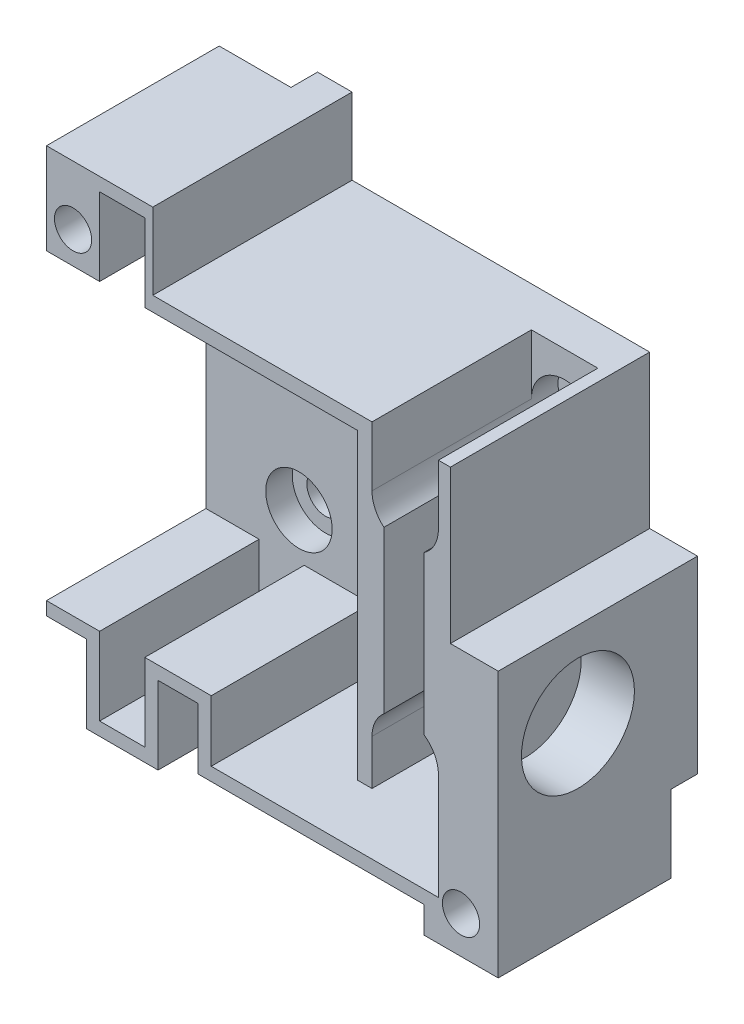
SolidWorks part; units mm, degrees
ref_plane "Front Plane" through (0, 0, 0) normal (0, 0, 1) x (1, 0, 0)
ref_plane "Top Plane" through (0, 0, 0) normal (0, 1, 0) x (1, 0, 0)
ref_plane "Right Plane" through (0, 0, 0) normal (1, 0, 0) x (0, 0, -1)
sketch "Sketch1" plane through (0, 0, 0) normal (0, 0, 1) x (1, 0, 0)
  line L1 (-17, 19) -> (17, 19)
  line L2 (-17, 19) -> (-17, -19)
  line L3 (-17, -19) -> (17, -19)
  line L4 (17, 19) -> (17, -19)
  line L5 (-17, 19) -> (17, -19) construction
  line L6 (-17, -19) -> (17, 19) construction
  point P0 (0, 0)
  dimension "D1" = 38
  dimension "D2" = 34
extrude "Boss-Extrude1" add sketch "Sketch1" along normal blind 16
sketch "Sketch2" plane through (0, 0, 16) normal (0, 0, 1) x (1, 0, 0)
  line L0 (0, 0) -> (-17, 0) construction
  line L5 (-17, 11.4) -> (5.4, 11.4)
  line L6 (-17, 11.4) -> (-17, -11.4)
  line L7 (-17, -11.4) -> (5.4, -11.4)
  line L8 (5.4, 11.4) -> (5.4, -11.4)
  line L9 (-17, 11.4) -> (5.4, -11.4) construction
  line L10 (-17, -11.4) -> (5.4, 11.4) construction
  line L11 (-17, 19) -> (-17, -19) construction
  line L12 (-10.6, -11.4) -> (-10.6, -16.25)
  line L13 (-13, 11.4) -> (-10.6, 11.4)
  line L14 (-13, 11.4) -> (-13, 16.25)
  line L15 (-13, 16.25) -> (-10.6, 16.25)
  line L16 (-10.6, 11.4) -> (-10.6, 16.25)
  line L17 (-13, -11.4) -> (-13, -16.25)
  line L18 (-13, -16.25) -> (-10.6, -16.25)
  line L21 (-17, -11.4) -> (-17, 4.4)
  point P0 (-5.8, 0)
  dimension "D1" = 22.4
  dimension "D2" = 22.8
  dimension "D3" = 5.8
  dimension "D4" = 4
  dimension "D5" = 2.4
  dimension "D6" = 4.85
extrude "Cut-Extrude1" cut sketch "Sketch2" against normal blind 13 contours L8 L5 L6 L7 | L17 L18 L12 L7 | L5 L16 L15 L14
sketch "Sketch3" plane through (0, 0, 16) normal (0, 0, 1) x (1, 0, 0)
  line L1 (5.4, -11.4) -> (-4.6, -11.4)
  line L2 (5.4, -11.4) -> (5.4, -16)
  line L3 (5.4, -16) -> (-4.6, -16)
  line L4 (-4.6, -11.4) -> (-4.6, -16)
  line L5 (5.4, -16) -> (8.4, -16)
  line L6 (5.4, -16) -> (5.4, -11.4)
  line L7 (5.4, -11.4) -> (8.4, -11.4)
  line L8 (8.4, -16) -> (8.4, -11.4)
  line L10 (-17, -19) -> (17, -19) construction
  line L11 (17, 19) -> (-17, 19) construction
  line L12 (8.4, -16) -> (11.4, -16)
  line L13 (8.4, -16) -> (8.4, 19)
  line L14 (8.4, 19) -> (11.4, 19)
  line L15 (11.4, -16) -> (11.4, 19)
  line M11 (17, 19) -> (-17, 19)
  line M21 (5.4, -11.4) -> (-10.6, -11.4)
  dimension "D1" = 3
  dimension "D2" = 10
  dimension "D3" = 3
  dimension "D4" = 3
extrude "Cut-Extrude2" cut sketch "Sketch3" against normal blind 13 contours L12 L15 L13 L8 M11 | L4 L3 L2 M21 | L5 L8 L7 L2
sketch "Sketch4" plane through (0, 0, 16) normal (0, 0, 1) x (1, 0, 0)
  line L0 (-17, 19) -> (-17, 11.4) construction
  line L3 (-17, -19) -> (17, -19) construction
  line L4 (17, -19) -> (17, 19) construction
  line L5 (8.4, 19) -> (-17, 19) construction
  circle A0 centre (-15, 13.8) radius 1.4
  circle A1 centre (14.2, -16.2) radius 1.4
  dimension "D2" = 5.2
  dimension "D3" = 2.8
  dimension "D4" = 2.8
  dimension "D5" = 2.8
  dimension "D6" = 2.8
  dimension "D1" = 2
extrude "Cut-Extrude3" cut sketch "Sketch4" against normal through all
sketch "Sketch5" plane through (0, 0, 0) normal (0, 0, -1) x (-1, 0, 0)
  line L0 (-17, 19) -> (17, 19) construction
  line L1 (18.4, 13.8) -> (11.6, 13.8)
  line L2 (18.4, 13.8) -> (18.4, 19)
  line L3 (18.4, 19) -> (11.6, 19)
  line L4 (11.6, 13.8) -> (11.6, 19)
  line L5 (-17, -19) -> (-17, 19) construction
  line L6 (-14.2, -19.2) -> (-17, -19.2)
  line L7 (-14.2, -19.2) -> (-14.2, -13.2)
  line L8 (-14.2, -13.2) -> (-17, -13.2)
  line L9 (-17, -19.2) -> (-17, -13.2)
  line L11 (-14.2, -19.2) -> (-10.2, -19.2)
  line L12 (-14.2, -19.2) -> (-14.2, -13.2)
  line L13 (-14.2, -13.2) -> (-10.2, -13.2)
  line L14 (-10.2, -19.2) -> (-10.2, -13.2)
  circle A0 centre (15, 13.8) radius 3.4
  circle A1 centre (-14.2, -16.2) radius 3
  circle M1 centre (15, 13.8) radius 1.4
  circle M2 centre (-14.2, -16.2) radius 1.4
  line M3 (-17, 19) -> (-17, -19)
  line M4 (-17, -19) -> (17, -19)
  line M5 (17, -19) -> (17, 19)
  line M6 (17, 19) -> (-17, 19)
  dimension "D1" = 6.8
  dimension "D2" = 6
  dimension "D3" = 4
extrude "Cut-Extrude5" cut sketch "Sketch5" against normal blind 2 contours A1 L7 M4 M2 | L7 A1 L9 M4 M2 | A1 M3 M4 | A1 L8 M3 | L9 A1 | A1 L7 M4 | A1 L9 L6 M4 | L7 A1 M4 | A0 L2 L3 M5 | A0 L4 M5 M6 | A0 L1 M5 M1 | L1 A0 M5 | A0 L1 M5 | L1 A0 M5 M1 | A1 L14 L13 M4
sketch "Sketch7" plane through (0, 19, 0) normal (0, 1, 0) x (1, 0, 0)
  line L0 (17, -16) -> (17, 0) construction
  line L1 (-17, -16) -> (17, -16)
  line L2 (-17, -16) -> (-17, -15)
  line L3 (-17, -15) -> (17, -15)
  line L4 (17, -16) -> (17, -15)
  dimension "D1" = 1
extrude "Cut-Extrude6" cut sketch "Sketch7" against normal through all
sketch "Sketch9" plane through (0, 0, 15) normal (0, 0, 1) x (1, 0, 0)
  line L0 (8.4, 19) -> (-17, 19) construction
  line L1 (-9, 19) -> (17, 19)
  line L2 (-9, 19) -> (-9, 12.5)
  line L3 (-9, 12.5) -> (17, 12.5)
  line L4 (17, 19) -> (17, 12.5)
  line L5 (17, -19) -> (17, 19) construction
  line L6 (-17, -19) -> (-17, -11.4) construction
  line L7 (-17, -12.4) -> (-14, -12.4)
  line L8 (-17, -12.4) -> (-17, -19)
  line L9 (-17, -19) -> (-14, -19)
  line L10 (-14, -12.4) -> (-14, -19)
  line L11 (17, -19) -> (-17, -19) construction
  line L12 (-13, -16.25) -> (-10.6, -16.25) construction
  line L13 (-8.6, -19) -> (-5.6, -19)
  line L14 (-8.6, -19) -> (-8.6, -12.4)
  line L15 (-8.6, -12.4) -> (-5.6, -12.4)
  line L16 (-5.6, -19) -> (-5.6, -12.4)
  line L17 (-5.6, -19) -> (11.4, -19)
  line L18 (-5.6, -19) -> (-5.6, -17)
  line L19 (-5.6, -17) -> (11.4, -17)
  line L20 (11.4, -19) -> (11.4, -17)
  line L21 (-14, -19) -> (-8.6, -19)
  line L22 (-14, -19) -> (-14, -18.25)
  line L23 (-10.6, -11.4) -> (-4.6, -11.4) construction
  line L24 (-17, -11.4) -> (-13, -11.4) construction
  line L25 (-10.6, -11.4) -> (-10.6, -16.25) construction
  line L26 (-4.6, -11.4) -> (-4.6, -16) construction
  line L27 (-4.6, -16) -> (11.4, -16) construction
  line L28 (-13, -11.4) -> (-13, -16.25) construction
  line L29 (-14, -18.25) -> (-8.6, -18.25)
  line L30 (-8.6, -19) -> (-8.6, -18.25)
  line L32 (-13, 16.25) -> (-10.6, 16.25) construction
  line L33 (-17, 19) -> (-9, 19)
  line L34 (-17, 19) -> (-17, 18.25)
  line L35 (-17, 18.25) -> (-9, 18.25)
  line L36 (-9, 19) -> (-9, 18.25)
  line L37 (11.4, -16) -> (11.4, 19) construction
  line L38 (17, 19) -> (13.4, 19)
  line L39 (17, 19) -> (17, 1)
  line L40 (17, 1) -> (13.4, 1)
  line L41 (13.4, 19) -> (13.4, 1)
  line M21 (8.4, -11.4) -> (8.4, 19)
  line M22 (8.4, 19) -> (-17, 19)
  line M23 (-17, 19) -> (-17, 11.4)
  dimension "D1" = 6.5
  dimension "D2" = 26
  dimension "D3" = 1
  dimension "D4" = 1
  dimension "D5" = 2
  dimension "D6" = 1
  dimension "D7" = 1
  dimension "D8" = 1
  dimension "D9" = 2
  dimension "D10" = 2
  dimension "D11" = 2
  dimension "D12" = 17
  dimension "D13" = 18
extrude "Cut-Extrude9" cut sketch "Sketch9" against normal through all contours L2 L3 M21 M22 | L35 L2 M23 M22 | L41 L1 L3 M21 | L1 L41 L3 L4 | L3 L41 L40 L39 | L17 L20 L19 L16 | L13 L16 L15 L14 | L29 L10 L21 L14 | L10 L7 L8 L9
sketch "Sketch10" plane through (0, 0, 3) normal (0, 0, 1) x (1, 0, 0)
  line L1 (-10, 8) -> (10, 8)
  line L2 (-10, 8) -> (-10, -8)
  line L3 (-10, -8) -> (10, -8)
  line L4 (10, 8) -> (10, -8)
  line L5 (-10, 8) -> (10, -8) construction
  line L6 (-10, -8) -> (10, 8) construction
  circle A0 centre (-10, 8) radius 2.5
  circle A1 centre (10, 8) radius 2.5
  circle A2 centre (-10, -8) radius 2.5
  circle A3 centre (10, -8) radius 2.5
  point P0 (0, 0)
  line M6 (8.4, 12.5) -> (8.4, -11.4)
  line M22 (11.4, -16) -> (11.4, 12.5)
  dimension "D3" = 5
  dimension "D1" = 20
  dimension "D2" = 16
extrude "Cut-Extrude10" cut sketch "Sketch10" against normal blind 2 and the other way through all contours L2 A0 L1 | L1 A0 L2 | A1 L4 L1 M6 | A1 L1 L4 M22 M6 | A1 M22 | A1 L1 M6 | L1 A1 M6 | L3 A2 L2 | L2 A2 L3 | A3 L4 L3 M22 M6 | A3 M22 | L4 A3 L3 M6 | A3 L3 M6 | L3 A3 M6
sketch "Sketch11" plane through (0, 0, 15) normal (0, 0, 1) x (1, 0, 0)
  line L5 (5.4, -11.4) -> (8.4, -11.4) construction
  line L6 (12.5, -8) -> (7.5, -8)
  line L7 (12.5, -8) -> (12.5, -11.4)
  line L8 (11.4, -11.4) -> (7.5, -11.4)
  line L9 (7.5, -8) -> (7.5, -11.4)
  line L10 (-9, 12.5) -> (8.4, 12.5) construction
  line L11 (12.5, 8) -> (7.5, 8)
  line L12 (12.5, 8) -> (12.5, 12.5)
  line L13 (12.5, 12.5) -> (7.5, 12.5)
  line L14 (7.5, 8) -> (7.5, 12.5)
  line L16 (11.4, -16) -> (12.5, -16)
  line L17 (11.4, -16) -> (11.4, -11.4)
  line L19 (12.5, -16) -> (12.5, -11.4)
  arc A0 (11.4, -10.0712) -> (11.4, -5.9288) centre (10, -8) ccw construction
  arc A1 (11.4, 5.9288) -> (11.4, 10.0712) centre (10, 8) ccw construction
extrude "Cut-Extrude11" cut sketch "Sketch11" against normal blind 12
sketch "Sketch12" plane through (0, 0, 15) normal (0, 0, 1) x (1, 0, 0)
  line L1 (-10.6, 11.4) -> (-9.6, 11.4)
  line L2 (-10.6, 11.4) -> (-10.6, 16.25)
  line L3 (-10.6, 16.25) -> (-9.6, 16.25)
  line L4 (-9.6, 11.4) -> (-9.6, 16.25)
  line L5 (-10.6, -11.4) -> (-9.6, -11.4)
  line L6 (-10.6, -11.4) -> (-10.6, -16.25)
  line L7 (-10.6, -16.25) -> (-9.6, -16.25)
  line L8 (-9.6, -11.4) -> (-9.6, -16.25)
  line L10 (5.4, -11.4) -> (6.4, -11.4)
  line L11 (5.4, -11.4) -> (5.4, 11.4)
  line L12 (5.4, 11.4) -> (6.4, 11.4)
  line L13 (6.4, -11.4) -> (6.4, 11.4)
  dimension "D1" = 1
  dimension "D2" = 1
  dimension "D3" = 4.85
  dimension "D4" = 4.85
  dimension "D5" = 1
extrude "Cut-Extrude12" cut sketch "Sketch12" against normal blind 12
sketch "Sketch14" plane through (17, 0, 0) normal (1, 0, 0) x (0, 0, -1)
  line L0 (-15, -19) -> (-15, 1) construction
  line L1 (-15, -19) -> (-2, -19) construction
  circle A0 centre (-9, -5.4) radius 4.25
  dimension "D1" = 8.5
  dimension "D2" = 6
  dimension "D3" = 13.6
extrude "Cut-Extrude13" cut sketch "Sketch14" against normal blind 4
sketch "Sketch17" plane through (0, 0, 15) normal (0, 0, 1) x (1, 0, 0)
  line L1 (-13, 16.25) -> (-9.6, 16.25)
  line L2 (-13, 16.25) -> (-13, 17.25)
  line L3 (-13, 17.25) -> (-9.6, 17.25)
  line L4 (-9.6, 16.25) -> (-9.6, 17.25)
  line L7 (-9.6, -16.25) -> (-13, -16.25)
  line L8 (-9.6, -16.25) -> (-9.6, -17.25)
  line L9 (-9.6, -17.25) -> (-13, -17.25)
  line L10 (-13, -16.25) -> (-13, -17.25)
  dimension "D1" = 1
  dimension "D2" = 3.4
  dimension "D3" = 1
  dimension "D4" = 3.4
extrude "Cut-Extrude16" cut sketch "Sketch17" against normal blind 12
sketch "Sketch18" plane through (0, 0, 1) normal (0, 0, 1) x (1, 0, 0)
  circle A1 centre (-10, 8) radius 1.4
  circle A2 centre (10, 8) radius 1.4
  circle A3 centre (-10, -8) radius 1.4
  circle A4 centre (10, -8) radius 1.4
  dimension "D1" = 2.8
  dimension "D2" = 2.8
  dimension "D3" = 2.8
  dimension "D4" = 2.8
extrude "Cut-Extrude17" cut sketch "Sketch18" against normal blind 12
